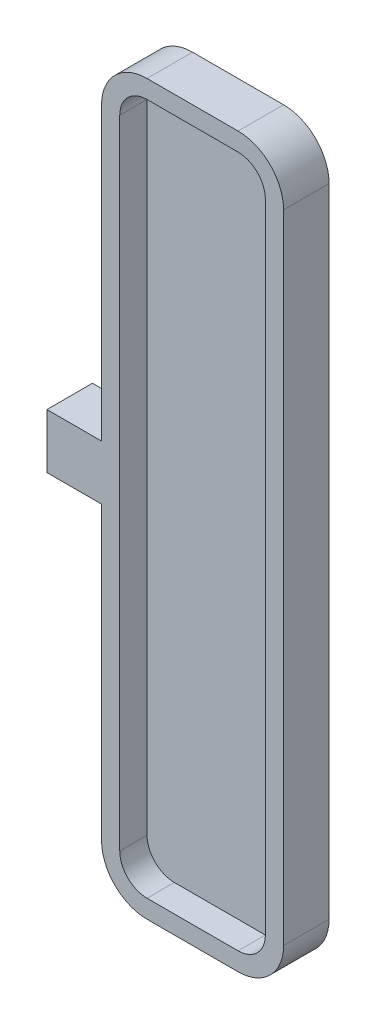
SolidWorks part; units mm, degrees
ref_plane "Front Plane" through (0, 0, 0) normal (0, 0, 1) x (1, 0, 0)
ref_plane "Top Plane" through (0, 0, 0) normal (0, 1, 0) x (1, 0, 0)
ref_plane "Right Plane" through (0, 0, 0) normal (1, 0, 0) x (0, 0, -1)
sketch "Sketch1" plane through (0, 0, 0) normal (0, 0, 1) x (1, 0, 0)
  line L1 (10, -40) -> (-10, -40)
  line L2 (10, -40) -> (10, 40)
  line L3 (10, 40) -> (-10, 40)
  line L4 (-10, -40) -> (-10, 40)
  line L5 (10, -40) -> (-10, 40) construction
  line L6 (10, 40) -> (-10, -40) construction
  point P0 (0, 0)
  dimension "D1" = 80
  dimension "D2" = 20
extrude "Boss-Extrude1" add sketch "Sketch1" along normal blind 5
fillet "Fillet1" radius 5 4 edges at (-10, -40, 2.5) (10, -40, 2.5) (10, 40, 2.5) (-10, 40, 2.5)
shell "Shell1" thickness 2
sketch "Sketch3" plane through (-10, 0, 0) normal (-1, 0, 0) x (0, 0, 1)
  line L0 (0, 0) -> (35.9622, 0) construction
  line L1 (0, 35) -> (0, -35) construction
  line L2 (5, 35) -> (5, -35) construction
  line L3 (5, 3) -> (0, 3)
  line L4 (5, 3) -> (5, -3)
  line L5 (5, -3) -> (0, -3)
  line L6 (0, 3) -> (0, -3)
  line L7 (5, 3) -> (0, -3) construction
  line L8 (5, -3) -> (0, 3) construction
  point P4 (2.5, 0)
  dimension "D1" = 6
  dimension "D2" = 5
extrude "Boss-Extrude3" add sketch "Sketch3" along normal blind 6
sketch "Sketch4" plane through (-16, 0, 0) normal (-1, 0, 0) x (0, 0, 1)
  line L0 (0, 0) -> (34.4711, 0) construction
  line L1 (0, 3) -> (0, -3) construction
  line L3 (2.5, 3) -> (2.5, -3) construction
  line L4 (5, 3) -> (0, 3) construction
  line L5 (0, -3) -> (5, -3) construction
  circle A0 centre (2.5, 0) radius 1.425
  dimension "D1" = 2.85
extrude "Cut-Extrude1" cut sketch "Sketch4" against normal blind 4
